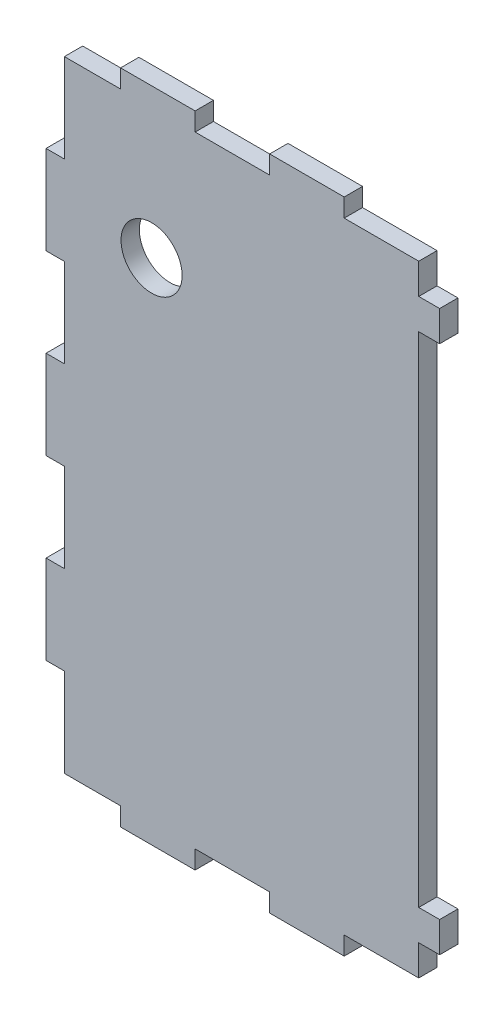
SolidWorks part; units mm, degrees
ref_plane "Alzado" through (0, 0, 0) normal (0, 0, 1) x (1, 0, 0)
ref_plane "Planta" through (0, 0, 0) normal (0, 1, 0) x (1, 0, 0)
ref_plane "Vista lateral" through (0, 0, 0) normal (1, 0, 0) x (0, 0, -1)
sketch "Croquis1" plane through (0, 0, 0) normal (0, 0, 1) x (1, 0, 0)
  line L0 (0, -17.0016) -> (0, -14.0016)
  line L1 (-48.39, -14.0016) -> (0, -14.0016) construction
  line L2 (0, -17.0016) -> (104.61, -17.0016)
  line L3 (101.61, -17.0016) -> (101.61, -49.332) construction
  line L4 (-227.956, -78.0016) -> (93.758, -78.0016) construction
  line L5 (-48.39, -14.0016) -> (-48.39, -78.0016) construction
  line L6 (78.6222, -39.0016) -> (-38.712, -39.0016) construction
  line L7 (0, -14.0016) -> (0, -17.0016) construction
  line L8 (0, -17.0016) -> (-48.39, -17.0016) construction
  line L9 (-48.39, -14.0016) -> (-38.712, -14.0016)
  line L10 (-38.712, -14.0016) -> (-38.712, -17.0016)
  line L11 (-38.712, -17.0016) -> (-29.034, -17.0016)
  line L12 (-29.034, -17.0016) -> (-29.034, -14.0016)
  line L13 (-29.034, -14.0016) -> (-19.356, -14.0016)
  line L14 (-19.356, -14.0016) -> (-19.356, -17.0016)
  line L15 (-19.356, -17.0016) -> (-9.678, -17.0016)
  line L16 (-9.678, -17.0016) -> (-9.678, -14.0016)
  line L17 (-9.678, -14.0016) -> (0, -14.0016)
  line L18 (104.61, -17.0016) -> (104.61, -78.0016) construction
  line L19 (104.61, -17.0016) -> (104.61, -29.2016)
  line L20 (104.61, -29.2016) -> (101.61, -29.2016)
  line L21 (101.61, -29.2016) -> (101.61, -41.4016)
  line L22 (101.61, -41.4016) -> (104.61, -41.4016)
  line L23 (104.61, -41.4016) -> (104.61, -53.6016)
  line L24 (104.61, -53.6016) -> (101.61, -53.6016)
  line L25 (101.61, -53.6016) -> (101.61, -65.8016)
  line L26 (101.61, -65.8016) -> (104.61, -65.8016)
  line L27 (104.61, -65.8016) -> (104.61, -78.0016)
  line L28 (-45.39, -56.5563) -> (-45.39, 45.6638) construction
  line L29 (-48.39, -14.0016) -> (-48.39, -26.8016)
  line L30 (-48.39, -26.8016) -> (-45.39, -26.8016)
  line L31 (-45.39, -26.8016) -> (-45.39, -39.6016)
  line L32 (-45.39, -39.6016) -> (-48.39, -39.6016)
  line L33 (-48.39, -39.6016) -> (-48.39, -52.4016)
  line L34 (-48.39, -52.4016) -> (-45.39, -52.4016)
  line L35 (-45.39, -52.4016) -> (-45.39, -65.2016)
  line L36 (-45.39, -65.2016) -> (-48.39, -65.2016)
  line L37 (-48.39, -65.2016) -> (-48.39, -78.0016)
  line L38 (-102.5031, -75.0016) -> (75.9308, -75.0016) construction
  line L39 (-124.386, -156.1001) -> (179.1879, -156.1001) construction
  line L40 (-48.39, -153.1001) -> (104.61, -153.1001) construction
  line L41 (-48.39, -78.0016) -> (-34.4809, -78.0016)
  line L42 (-34.4809, -78.0016) -> (-34.4809, -75.0016)
  line L43 (-34.4809, -75.0016) -> (-20.5718, -75.0016)
  line L44 (-20.5718, -75.0016) -> (-20.5718, -78.0016)
  line L45 (-20.5718, -78.0016) -> (-6.6627, -78.0016)
  line L46 (-6.6627, -78.0016) -> (-6.6627, -75.0016)
  line L47 (-6.6627, -75.0016) -> (7.2464, -75.0016)
  line L48 (7.2464, -75.0016) -> (7.2464, -78.0016)
  line L49 (7.2464, -78.0016) -> (21.1555, -78.0016)
  line L50 (21.1555, -78.0016) -> (21.1555, -75.0016)
  line L51 (21.1555, -75.0016) -> (35.0645, -75.0016)
  line L52 (35.0645, -75.0016) -> (35.0645, -78.0016)
  line L53 (35.0645, -78.0016) -> (48.9736, -78.0016)
  line L54 (48.9736, -78.0016) -> (48.9736, -75.0016)
  line L55 (48.9736, -75.0016) -> (62.8827, -75.0016)
  line L56 (62.8827, -75.0016) -> (62.8827, -78.0016)
  line L57 (62.8827, -78.0016) -> (76.7918, -78.0016)
  line L58 (76.7918, -78.0016) -> (76.7918, -75.0016)
  line L59 (76.7918, -75.0016) -> (90.7009, -75.0016)
  line L60 (90.7009, -75.0016) -> (90.7009, -78.0016)
  line L61 (90.7009, -78.0016) -> (104.61, -78.0016)
  line L62 (-48.39, -153.1001) -> (-48.39, -260.7101) construction
  line L63 (-48.39, -260.7101) -> (104.61, -260.7101) construction
  line L64 (104.61, -153.1001) -> (104.61, -260.7101) construction
  line L65 (-68.7634, -257.7101) -> (144.8732, -257.7101) construction
  line L66 (101.61, -78.0016) -> (101.61, -269.1968) construction
  line L67 (-45.39, -153.1001) -> (-45.39, -251.8965) construction
  line L68 (-34.4809, -78.0016) -> (-34.4809, -243.0877) construction
  line L69 (-20.5718, -78.0016) -> (-20.5718, -243.0877) construction
  line L70 (-6.6627, -75.0016) -> (-6.6627, -243.0877) construction
  line L71 (7.2464, -75.0016) -> (7.2464, -243.0877) construction
  line L72 (21.1555, -75.0016) -> (21.1555, -243.0877) construction
  line L73 (35.0645, -75.0016) -> (35.0645, -243.0877) construction
  line L74 (48.9736, -75.0016) -> (48.9736, -243.0877) construction
  line L75 (62.8827, -75.0016) -> (62.8827, -243.0877) construction
  line L76 (76.7918, -75.0016) -> (76.7918, -243.0877) construction
  line L77 (90.7009, -75.0016) -> (90.7009, -243.0877) construction
  line L78 (-34.4809, -156.1001) -> (-48.39, -156.1001)
  line L79 (-34.4809, -156.1001) -> (-34.4809, -153.1001)
  line L80 (-34.4809, -153.1001) -> (-20.5718, -153.1001)
  line L81 (-20.5718, -153.1001) -> (-20.5718, -156.1001)
  line L82 (-20.5718, -156.1001) -> (-6.6627, -156.1001)
  line L83 (-6.6627, -156.1001) -> (-6.6627, -153.1001)
  line L84 (-6.6627, -153.1001) -> (7.2464, -153.1001)
  line L85 (7.2464, -153.1001) -> (7.2464, -156.1001)
  line L86 (7.2464, -156.1001) -> (21.1555, -156.1001)
  line L87 (21.1555, -156.1001) -> (21.1555, -153.1001)
  line L88 (21.1555, -153.1001) -> (35.0645, -153.1001)
  line L89 (35.0645, -153.1001) -> (35.0645, -156.1001)
  line L90 (35.0645, -156.1001) -> (48.9736, -156.1001)
  line L91 (48.9736, -156.1001) -> (48.9736, -153.1001)
  line L92 (48.9736, -153.1001) -> (62.8827, -153.1001)
  line L93 (62.8827, -153.1001) -> (62.8827, -156.1001)
  line L94 (62.8827, -156.1001) -> (76.7918, -156.1001)
  line L95 (76.7918, -156.1001) -> (76.7918, -153.1001)
  line L96 (76.7918, -153.1001) -> (90.7009, -153.1001)
  line L97 (90.7009, -153.1001) -> (90.7009, -156.1001)
  line L98 (90.7009, -156.1001) -> (104.61, -156.1001)
  line L99 (-48.39, -257.7101) -> (-34.4809, -257.7101)
  line L100 (-34.4809, -257.7101) -> (-34.4809, -260.7101)
  line L101 (-34.4809, -260.7101) -> (-20.5718, -260.7101)
  line L102 (-20.5718, -260.7101) -> (-20.5718, -257.7101)
  line L103 (-20.5718, -257.7101) -> (-6.6627, -257.7101)
  line L104 (-6.6627, -257.7101) -> (-6.6627, -260.7101)
  line L105 (-6.6627, -260.7101) -> (7.2464, -260.7101)
  line L106 (7.2464, -260.7101) -> (7.2464, -257.7101)
  line L107 (7.2464, -257.7101) -> (21.1555, -257.7101)
  line L108 (21.1555, -257.7101) -> (21.1555, -260.7101)
  line L109 (21.1555, -260.7101) -> (35.0645, -260.7101)
  line L110 (35.0645, -260.7101) -> (35.0645, -257.7101)
  line L111 (35.0645, -257.7101) -> (48.9736, -257.7101)
  line L112 (48.9736, -257.7101) -> (48.9736, -260.7101)
  line L113 (48.9736, -260.7101) -> (62.8827, -260.7101)
  line L114 (62.8827, -260.7101) -> (62.8827, -257.7101)
  line L115 (62.8827, -257.7101) -> (76.7918, -257.7101)
  line L116 (76.7918, -257.7101) -> (76.7918, -260.7101)
  line L117 (76.7918, -260.7101) -> (90.7009, -260.7101)
  line L118 (90.7009, -260.7101) -> (90.7009, -257.7101)
  line L119 (90.7009, -257.7101) -> (104.61, -257.7101)
  line L120 (-226.2526, -14.0016) -> (-226.2526, -78.0016) construction
  line L121 (-290.2526, -78.0016) -> (-226.2526, -78.0016) construction
  line L122 (-226.2526, -78.0016) -> (-226.2526, -287.7111) construction
  line L123 (-290.2526, -78.0016) -> (-290.2526, -287.7111) construction
  line L124 (-290.2526, -287.7111) -> (-226.2526, -287.7111) construction
  line L125 (-48.39, -26.8016) -> (-105.5506, -26.8016) construction
  line L126 (-48.39, -39.6016) -> (-94.7516, -39.6016) construction
  line L127 (-48.39, -52.4016) -> (-71.8061, -52.4016) construction
  line L128 (-48.39, -65.2016) -> (-67.7461, -65.2016) construction
  line L129 (-277.4526, -73.8444) -> (-277.4526, -111.8004) construction
  line L130 (-264.6526, -73.8444) -> (-264.6526, -111.8004) construction
  line L131 (-251.8526, -90.832) -> (-251.8526, -128.788) construction
  line L132 (-239.0526, -73.8444) -> (-239.0526, -111.8004) construction
  line L133 (-229.2526, -73.8444) -> (-229.2526, -93.389) construction
  line L134 (165.3571, -156.1001) -> (174.5571, -156.1001)
  line L135 (174.5571, -156.1001) -> (174.5571, -153.1001)
  line L136 (174.5571, -153.1001) -> (186.7571, -153.1001)
  line L137 (186.7571, -153.1001) -> (186.7571, -156.1001)
  line L138 (186.7571, -156.1001) -> (198.9571, -156.1001)
  line L139 (198.9571, -156.1001) -> (198.9571, -153.1001)
  line L140 (198.9571, -153.1001) -> (211.1571, -153.1001)
  line L141 (211.1571, -153.1001) -> (211.1571, -156.1001)
  line L142 (211.1571, -156.1001) -> (223.3571, -156.1001)
  line L143 (-229.2526, -156.1001) -> (-229.2526, -170.6158)
  line L144 (-229.2526, -170.6158) -> (-226.2526, -170.6158)
  line L145 (-226.2526, -170.6158) -> (-226.2526, -185.1315)
  line L146 (-226.2526, -185.1315) -> (-229.2526, -185.1315)
  line L147 (-229.2526, -185.1315) -> (-229.2526, -199.6473)
  line L148 (-229.2526, -199.6473) -> (-226.2526, -199.6473)
  line L149 (-226.2526, -199.6473) -> (-226.2526, -220.163)
  line L150 (-226.2526, -220.163) -> (-229.2526, -220.163)
  line L151 (-48.39, -257.7101) -> (-48.39, -243.1944)
  line L152 (-48.39, -243.1944) -> (-45.39, -243.1944)
  line L153 (-45.39, -243.1944) -> (-45.39, -228.6787)
  line L154 (-45.39, -228.6787) -> (-48.39, -228.6787)
  line L155 (-48.39, -228.6787) -> (-48.39, -214.163)
  line L156 (-48.39, -214.163) -> (-45.39, -214.163)
  line L157 (-45.39, -214.163) -> (-45.39, -199.6473)
  line L158 (-45.39, -199.6473) -> (-48.39, -199.6473)
  line L159 (-48.39, -199.6473) -> (-48.39, -185.1315)
  line L160 (-48.39, -185.1315) -> (-45.39, -185.1315)
  line L161 (-45.39, -185.1315) -> (-45.39, -170.6158)
  line L162 (-45.39, -170.6158) -> (-48.39, -170.6158)
  line L163 (-48.39, -170.6158) -> (-48.39, -156.1001)
  line L164 (-48.39, -228.6787) -> (-80.3979, -228.6787) construction
  line L165 (-48.39, -243.1944) -> (-76.899, -243.1944) construction
  line L166 (-48.39, -214.163) -> (-74.7996, -214.163) construction
  line L167 (-48.39, -199.6473) -> (-74.7996, -199.6473) construction
  line L168 (-74.7996, -185.1315) -> (-48.39, -185.1315) construction
  line L169 (-48.39, -170.6158) -> (-71.0675, -170.6158) construction
  line L170 (-229.2526, -220.163) -> (-229.2526, -234.6787)
  line L171 (-287.2526, -73.8444) -> (-287.2526, -109.848) construction
  line L172 (-229.2526, -234.6787) -> (-226.2526, -234.6787)
  line L173 (-226.2526, -234.6787) -> (-226.2526, -249.1944)
  line L174 (-226.2526, -249.1944) -> (-229.2526, -249.1944)
  line L175 (-229.2526, -249.1944) -> (-229.2526, -257.7101)
  line L176 (223.3571, -257.7101) -> (211.1571, -257.7101)
  line L177 (211.1571, -257.7101) -> (211.1571, -260.7101)
  line L178 (211.1571, -260.7101) -> (198.9571, -260.7101)
  line L179 (198.9571, -260.7101) -> (198.9571, -257.7101)
  line L180 (198.9571, -257.7101) -> (186.7571, -257.7101)
  line L181 (186.7571, -257.7101) -> (186.7571, -260.7101)
  line L182 (186.7571, -260.7101) -> (174.5571, -260.7101)
  line L183 (174.5571, -260.7101) -> (174.5571, -257.7101)
  line L184 (-287.2526, -257.7101) -> (-287.2526, -243.1944)
  line L185 (-287.2526, -243.1944) -> (-290.2526, -243.1944)
  line L186 (-290.2526, -243.1944) -> (-290.2526, -228.6787)
  line L187 (-290.2526, -228.6787) -> (-287.2526, -228.6787)
  line L188 (-287.2526, -228.6787) -> (-287.2526, -214.163)
  line L189 (-287.2526, -214.163) -> (-290.2526, -214.163)
  line L190 (-290.2526, -214.163) -> (-290.2526, -199.6473)
  line L191 (-290.2526, -199.6473) -> (-287.2526, -199.6473)
  line L192 (-287.2526, -199.6473) -> (-287.2526, -185.1315)
  line L193 (-287.2526, -185.1315) -> (-290.2526, -185.1315)
  line L194 (-290.2526, -185.1315) -> (-290.2526, -170.6158)
  line L195 (-290.2526, -170.6158) -> (-287.2526, -170.6158)
  line L196 (-287.2526, -170.6158) -> (-287.2526, -156.1001)
  line L197 (174.5571, -257.7101) -> (165.3571, -257.7101)
  line L198 (-315.487, -120.5373) -> (-315.487, -274.6014) construction
  line L199 (-423.097, -153.1001) -> (-423.097, -80.2802) construction
  line L200 (-420.097, -153.1001) -> (-420.097, -73.0846) construction
  line L201 (-405.5813, -153.1001) -> (-405.5813, -73.0846) construction
  line L202 (-391.0655, -153.1001) -> (-391.0655, -77.6291) construction
  line L203 (-376.5498, -153.1001) -> (-376.5498, -80.2802) construction
  line L204 (-362.0341, -153.1001) -> (-362.0341, -73.0846) construction
  line L205 (-347.5184, -153.1001) -> (-347.5184, -77.6291) construction
  line L206 (-333.0027, -153.1001) -> (-333.0027, -73.0846) construction
  line L207 (-318.487, -153.1001) -> (-318.487, -77.6291) construction
  line L208 (-48.39, -21.6772) -> (-48.39, 38.9813) construction
  line L209 (-38.712, -14.0016) -> (-38.712, 45.6638) construction
  line L210 (-29.034, -14.0016) -> (-29.034, 45.6638) construction
  line L211 (-19.356, -14.0016) -> (-19.356, 45.6638) construction
  line L212 (-9.678, -14.0016) -> (-9.678, 45.6638) construction
  line L213 (0, -14.0016) -> (0, 45.6638) construction
  line L214 (2.5149, 38.1832) -> (-48.39, 38.1832) construction
  line L215 (-48.39, 86.5732) -> (-80.1148, 86.5732) construction
  line L216 (-48.39, 76.8952) -> (-75.2531, 76.8952) construction
  line L217 (-48.39, 67.2172) -> (-75.2531, 67.2172) construction
  line L218 (-48.39, 57.5392) -> (-80.1148, 57.5392) construction
  line L219 (-48.39, 47.8612) -> (-84.9766, 47.8612) construction
  line L220 (-318.487, 38.1832) -> (-318.487, 47.8612)
  line L221 (-48.39, 38.1832) -> (-76.9441, 38.1832) construction
  line L222 (-318.487, 47.8612) -> (-315.487, 47.8612)
  line L223 (-315.487, 47.8612) -> (-315.487, 57.5392)
  line L224 (-315.487, 57.5392) -> (-318.487, 57.5392)
  line L225 (-318.487, 57.5392) -> (-318.487, 67.2172)
  line L226 (-318.487, 67.2172) -> (-315.487, 67.2172)
  line L227 (-315.487, 67.2172) -> (-315.487, 76.8952)
  line L228 (-315.487, 76.8952) -> (-318.487, 76.8952)
  line L229 (-318.487, 76.8952) -> (-318.487, 86.5732)
  line L230 (-318.487, 86.5732) -> (-420.097, 86.5732)
  line L231 (-420.097, 86.5732) -> (-420.097, 76.8952)
  line L232 (-420.097, 76.8952) -> (-423.097, 76.8952)
  line L233 (-423.097, 76.8952) -> (-423.097, 67.2172)
  line L234 (-423.097, 67.2172) -> (-420.097, 67.2172)
  line L235 (-420.097, 67.2172) -> (-420.097, 57.5392)
  line L236 (-420.097, 57.5392) -> (-423.097, 57.5392)
  line L237 (-423.097, 57.5392) -> (-423.097, 47.8612)
  line L238 (-423.097, 47.8612) -> (-420.097, 47.8612)
  line L239 (-420.097, 47.8612) -> (-420.097, 38.1832)
  line L240 (-48.39, 41.1832) -> (-83.9517, 41.1832) construction
  line L241 (-318.487, 38.1832) -> (-333.0027, 38.1832)
  line L242 (-333.0027, 38.1832) -> (-333.0027, 41.1832)
  line L243 (-333.0027, 41.1832) -> (-347.5184, 41.1832)
  line L244 (-347.5184, 41.1832) -> (-347.5184, 38.1832)
  line L245 (-347.5184, 38.1832) -> (-362.0341, 38.1832)
  line L246 (-362.0341, 38.1832) -> (-362.0341, 41.1832)
  line L247 (-362.0341, 41.1832) -> (-376.5498, 41.1832)
  line L248 (-376.5498, 41.1832) -> (-376.5498, 38.1832)
  line L249 (-376.5498, 38.1832) -> (-391.0655, 38.1832)
  line L250 (-391.0655, 38.1832) -> (-391.0655, 41.1832)
  line L251 (-391.0655, 41.1832) -> (-405.5813, 41.1832)
  line L252 (-405.5813, 41.1832) -> (-405.5813, 38.1832)
  line L253 (-405.5813, 38.1832) -> (-420.097, 38.1832)
  line L254 (162.3571, -15.1529) -> (162.3571, -104.9762) construction
  line L255 (104.61, -29.2016) -> (145.8916, -29.2016) construction
  line L256 (104.61, -41.4016) -> (145.8916, -41.4016) construction
  line L257 (104.61, -65.8016) -> (131.4417, -65.8016) construction
  line L258 (104.61, -53.6016) -> (126.5441, -53.6016) construction
  line L259 (165.3571, -73.8444) -> (165.3571, -106.8492) construction
  line L260 (174.5571, -73.8444) -> (174.5571, -108.8044) construction
  line L261 (186.7571, -73.8444) -> (186.7571, -108.8044) construction
  line L262 (198.9571, -73.8444) -> (198.9571, -108.8044) construction
  line L263 (211.1571, -73.8444) -> (211.1571, -106.8492) construction
  line L264 (223.3571, -73.8444) -> (223.3571, -108.8044) construction
  line L265 (104.61, -257.7101) -> (104.61, -243.0877)
  line L266 (104.61, -243.0877) -> (101.61, -243.0877)
  line L267 (101.61, -243.0877) -> (101.61, -228.6787)
  line L268 (101.61, -228.6787) -> (104.61, -228.6787)
  line L269 (104.61, -228.6787) -> (104.61, -214.163)
  line L270 (104.61, -214.163) -> (101.61, -214.163)
  line L271 (101.61, -214.163) -> (101.61, -199.6473)
  line L272 (101.61, -199.6473) -> (104.61, -199.6473)
  line L273 (104.61, -199.6473) -> (104.61, -185.1315)
  line L274 (104.61, -185.1315) -> (101.61, -185.1315)
  line L275 (101.61, -185.1315) -> (101.61, -170.6158)
  line L276 (101.61, -170.6158) -> (104.61, -170.6158)
  line L277 (104.61, -170.6158) -> (104.61, -156.1001)
  line L278 (-229.2526, -156.1001) -> (-239.0526, -156.1001)
  line L279 (-239.0526, -156.1001) -> (-239.0526, -153.1001)
  line L280 (-239.0526, -153.1001) -> (-251.8526, -153.1001)
  line L281 (-251.8526, -153.1001) -> (-251.8526, -156.1001)
  line L282 (-251.8526, -156.1001) -> (-264.6526, -156.1001)
  line L283 (-264.6526, -156.1001) -> (-264.6526, -153.1001)
  line L284 (-264.6526, -153.1001) -> (-277.4526, -153.1001)
  line L285 (-277.4526, -153.1001) -> (-277.4526, -156.1001)
  line L286 (-277.4526, -156.1001) -> (-287.2526, -156.1001)
  line L287 (223.3571, -156.1001) -> (223.3571, -161.1001)
  line L288 (-229.2526, -257.7101) -> (-239.0526, -257.7101)
  line L289 (-239.0526, -257.7101) -> (-239.0526, -260.7101)
  line L290 (-239.0526, -260.7101) -> (-251.8526, -260.7101)
  line L291 (-251.8526, -260.7101) -> (-251.8526, -257.7101)
  line L292 (-251.8526, -257.7101) -> (-264.6526, -257.7101)
  line L293 (-264.6526, -257.7101) -> (-264.6526, -260.7101)
  line L294 (-264.6526, -260.7101) -> (-277.4526, -260.7101)
  line L295 (-277.4526, -260.7101) -> (-277.4526, -257.7101)
  line L296 (-277.4526, -257.7101) -> (-287.2526, -257.7101)
  line L297 (165.3571, -257.7101) -> (165.3571, -243.1944)
  line L298 (165.3571, -243.1944) -> (162.3571, -243.1944)
  line L299 (162.3571, -243.1944) -> (162.3571, -228.6787)
  line L300 (162.3571, -228.6787) -> (165.3571, -228.6787)
  line L301 (165.3571, -228.6787) -> (165.3571, -214.163)
  line L302 (165.3571, -214.163) -> (162.3571, -214.163)
  line L303 (162.3571, -214.163) -> (162.3571, -199.6473)
  line L304 (162.3571, -199.6473) -> (165.3571, -199.6473)
  line L305 (165.3571, -199.6473) -> (165.3571, -185.1315)
  line L306 (165.3571, -185.1315) -> (162.3571, -185.1315)
  line L307 (162.3571, -185.1315) -> (162.3571, -170.6158)
  line L308 (162.3571, -170.6158) -> (165.3571, -170.6158)
  line L309 (165.3571, -170.6158) -> (165.3571, -156.1001)
  line L310 (223.3571, -161.1001) -> (226.7768, -161.1001)
  line L315 (226.7768, -161.1001) -> (226.7768, -166.1001)
  line L316 (226.7768, -166.1001) -> (223.3571, -166.1001)
  line L317 (223.3571, -170.6158) -> (223.3571, -247.7101)
  line L318 (223.3571, -247.7101) -> (226.7768, -247.7101)
  line L319 (226.7768, -247.7101) -> (226.7768, -252.7101)
  line L320 (226.7768, -252.7101) -> (223.3571, -252.7101)
  line L321 (223.3571, -252.7101) -> (223.3571, -257.7101)
  line L322 (223.3571, -166.1001) -> (223.3571, -170.6158)
  circle A0 centre (73.11, -39.0016) radius 1.25
  circle A1 centre (31.5, -39.0016) radius 1.25
  circle A2 centre (-28.49, -39.0016) radius 1.25
  arc A3 (-226.2526, -65.2016) -> (-239.0526, -78.0016) centre (-226.2526, -78.0016) ccw construction
  arc A4 (-226.2526, -52.4016) -> (-251.8526, -78.0016) centre (-226.2526, -78.0016) ccw construction
  arc A5 (-226.2526, -39.6016) -> (-264.6526, -78.0016) centre (-226.2526, -78.0016) ccw construction
  arc A6 (-226.2526, -26.8016) -> (-277.4526, -78.0016) centre (-226.2526, -78.0016) ccw construction
  arc A7 (-226.2526, -14.0016) -> (-290.2526, -78.0016) centre (-226.2526, -78.0016) ccw construction
  arc A8 (-226.2526, -75.0016) -> (-229.2526, -78.0016) centre (-226.2526, -78.0016) ccw construction
  arc A9 (-226.2526, -17.0016) -> (-287.2526, -78.0016) centre (-226.2526, -78.0016) ccw construction
  arc A10 (-315.487, -156.1001) -> (-318.487, -153.1001) centre (-315.487, -153.1001) cw construction
  arc A11 (-315.487, -170.6158) -> (-333.0027, -153.1001) centre (-315.487, -153.1001) cw construction
  arc A12 (-315.487, -185.1315) -> (-347.5184, -153.1001) centre (-315.487, -153.1001) cw construction
  arc A13 (-315.487, -199.6473) -> (-362.0341, -153.1001) centre (-315.487, -153.1001) cw construction
  arc A14 (-315.487, -214.163) -> (-376.5498, -153.1001) centre (-315.487, -153.1001) cw construction
  arc A15 (-315.487, -228.6787) -> (-391.0655, -153.1001) centre (-315.487, -153.1001) cw construction
  arc A16 (-315.487, -243.1944) -> (-405.5813, -153.1001) centre (-315.487, -153.1001) cw construction
  arc A17 (-315.487, -257.7101) -> (-420.097, -153.1001) centre (-315.487, -153.1001) cw construction
  arc A18 (-315.487, -260.7101) -> (-423.097, -153.1001) centre (-315.487, -153.1001) cw construction
  arc A19 (-45.39, 38.1832) -> (-48.39, 41.1832) centre (-48.39, 38.1832) ccw construction
  arc A20 (-38.712, 38.1832) -> (-48.39, 47.8612) centre (-48.39, 38.1832) ccw construction
  arc A21 (-29.034, 38.1832) -> (-48.39, 57.5392) centre (-48.39, 38.1832) ccw construction
  arc A22 (-19.356, 38.1832) -> (-48.39, 67.2172) centre (-48.39, 38.1832) ccw construction
  arc A23 (-9.678, 38.1832) -> (-48.39, 76.8952) centre (-48.39, 38.1832) ccw construction
  arc A24 (0, 38.1832) -> (-48.39, 86.5732) centre (-48.39, 38.1832) ccw construction
  arc A25 (162.3571, -75.0016) -> (165.3571, -78.0016) centre (162.3571, -78.0016) cw construction
  arc A26 (162.3571, -65.8016) -> (174.5571, -78.0016) centre (162.3571, -78.0016) cw construction
  arc A27 (162.3571, -53.6016) -> (186.7571, -78.0016) centre (162.3571, -78.0016) cw construction
  arc A28 (162.3571, -41.4016) -> (198.9571, -78.0016) centre (162.3571, -78.0016) cw construction
  arc A29 (162.3571, -29.2016) -> (211.1571, -78.0016) centre (162.3571, -78.0016) cw construction
  arc A30 (162.3571, -17.0016) -> (223.3571, -78.0016) centre (162.3571, -78.0016) cw construction
  circle A31 centre (179.6281, -177.4981) radius 5
  text T0 "TOP\r\n"
  dimension "D2" = 2.5
  dimension "D3" = 2.5
  dimension "D4" = 2.5
  dimension "D7" = 101.6
  dimension "D20" = 22
  dimension "D9" = 36
  dimension "D1" = 153
  dimension "D5" = 3
  dimension "D6" = 104.61
  dimension "D8" = 3
  dimension "D10" = 3
  dimension "D11" = 41.61
  dimension "D13" = 3
  dimension "D14" = 153
  dimension "D15" = 107.61
  dimension "D17" = 3
  dimension "D18" = 3
  dimension "D19" = 28.5
  dimension "D21" = 5
  dimension "D22" = 5
  dimension "D23" = 5
  dimension "D24" = 5
extrude "Saliente-Extruir1" add sketch "Croquis1" along normal blind 3
